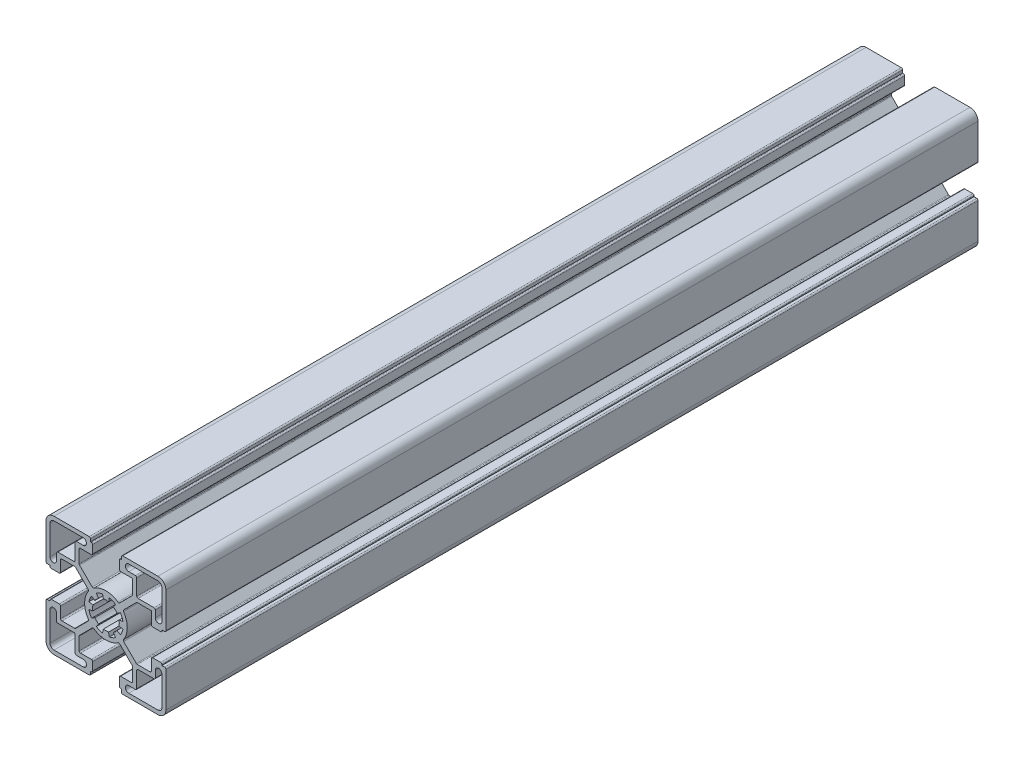
SolidWorks part; units mm, degrees
ref_plane "Front Plane" through (0, 0, 0) normal (0, 0, 1) x (1, 0, 0)
ref_plane "Top Plane" through (0, 0, 0) normal (0, 1, 0) x (1, 0, 0)
ref_plane "Right Plane" through (0, 0, 0) normal (1, 0, 0) x (0, 0, -1)
sketch "Sketch1" plane through (0, 0, 0) normal (0, 0, 1) x (1, 0, 0)
  line L0 (0, 22.5) -> (0, -22.5) construction
  line L1 (22.5, 0) -> (-22.5, 0) construction
  line L2 (-5.8, 22.5) -> (5.8, 22.5) construction
  line L3 (-5, 21) -> (5, 21) construction
  line L4 (-10.05, 10.05) -> (10.05, 10.05) construction
  line L5 (0, 0) -> (-10.05, 10.05) construction
  circle A0 centre (0, 0) radius 5 construction
  point P4 (0, 0)
  point P8 (0, 0)
  point P10 (0, 8)
  point P14 (0, 22.5)
  point P17 (0, 21)
  point P19 (0, 10.05)
sketch "Sketch2" plane through (0, 0, 0) normal (1, 0, 0) x (0, 0, -1)
  line L0 (152.4, 0) -> (-152.4, 0) construction
  point P4 (0, 0)
  dimension "D1" = 304.8
sketch "Sketch3" plane through (0, 0, 0) normal (0, 0, 1) x (1, 0, 0)
  line L5 (-21, 8.5375) -> (-21, 19.5)
  line L9 (0, 0) -> (-22.5, 22.5) construction
  line L10 (-11.55, -10.05) -> (-6.3569, -4.8569)
  line L11 (-19.5, 21) -> (-8.5375, 21)
  line L38 (-5.8, 22.5) -> (-5.8, 21)
  line L46 (-5.8, 21) -> (-5, 21)
  line L62 (-5, 21) -> (-5, 17.025)
  line L74 (-5, 17.025) -> (-10.05, 17.025)
  line L76 (-10.05, 17.025) -> (-10.05, 11.55)
  line L77 (-10.05, 11.55) -> (-4.8569, 6.3569)
  line L78 (-18.525, 8.5375) -> (-18.525, 11.55)
  line L79 (-10.05, 17.025) -> (-10.05, 22.5) construction
  line L80 (0, 22.5) -> (0, -22.5) construction
  line L81 (-5.8, 22.5) -> (5.8, 22.5) construction
  line L82 (10.05, 11.55) -> (4.8569, 6.3569)
  line L83 (10.05, 17.025) -> (10.05, 11.55)
  line L84 (5, 17.025) -> (10.05, 17.025)
  line L85 (5, 21) -> (5, 17.025)
  line L86 (5.8, 21) -> (5, 21)
  line L87 (5.8, 22.5) -> (5.8, 21)
  line L88 (-22.5, -5.8) -> (-21, -5.8)
  line L89 (-21, -5.8) -> (-21, -5)
  line L90 (-21, -5) -> (-17.025, -5)
  line L91 (-17.025, -5) -> (-17.025, -10.05)
  line L92 (-17.025, -10.05) -> (-11.55, -10.05)
  line L93 (-11.55, -10.05) -> (-6.3569, -4.8569)
  line L94 (-11.55, 10.05) -> (-6.3569, 4.8569)
  line L95 (-17.025, 10.05) -> (-11.55, 10.05)
  line L96 (-17.025, 5) -> (-17.025, 10.05)
  line L97 (-21, 5) -> (-17.025, 5)
  line L98 (-21, 5.8) -> (-21, 5)
  line L99 (-22.5, 5.8) -> (-21, 5.8)
  line L100 (-22.5, 5.8) -> (-22.5, 19.5)
  line L101 (-19.5, 22.5) -> (-5.8, 22.5)
  line L102 (-18.525, 11.55) -> (-11.55, 11.55)
  line L103 (-8.5375, 18.525) -> (-11.55, 18.525)
  line L104 (-11.55, 18.525) -> (-11.55, 11.55)
  line L108 (5.8, -22.5) -> (5.8, -21)
  line L113 (5.8, -21) -> (5, -21)
  line L117 (5.8, 22.5) -> (19.5, 22.5)
  line L118 (22.5, 19.5) -> (22.5, 5.8)
  line L119 (19.5, -22.5) -> (5.8, -22.5)
  line L120 (0, 0) -> (22.5, 0) construction
  line L121 (-22.5, -19.5) -> (-22.5, -5.8)
  line L136 (5, -21) -> (5, -17.025)
  line L137 (5, -17.025) -> (10.05, -17.025)
  line L138 (10.05, -17.025) -> (10.05, -11.55)
  line L139 (10.05, -11.55) -> (4.8569, -6.3569)
  line L140 (-10.05, -11.55) -> (-4.8569, -6.3569)
  line L141 (-10.05, -17.025) -> (-10.05, -11.55)
  line L142 (-5, -17.025) -> (-10.05, -17.025)
  line L143 (-5, -21) -> (-5, -17.025)
  line L144 (-5.8, -21) -> (-5, -21)
  line L145 (-5.8, -22.5) -> (-5.8, -21)
  line L146 (-5.8, -22.5) -> (-19.5, -22.5)
  line L147 (22.5, 5.8) -> (21, 5.8)
  line L148 (21, 5.8) -> (21, 5)
  line L149 (21, 5) -> (17.025, 5)
  line L150 (17.025, 5) -> (17.025, 10.05)
  line L151 (17.025, 10.05) -> (11.55, 10.05)
  line L152 (11.55, 10.05) -> (6.3569, 4.8569)
  line L153 (11.55, -10.05) -> (6.3569, -4.8569)
  line L154 (17.025, -10.05) -> (11.55, -10.05)
  line L155 (17.025, -5) -> (17.025, -10.05)
  line L156 (21, -5) -> (17.025, -5)
  line L157 (21, -5.8) -> (21, -5)
  line L158 (22.5, -5.8) -> (21, -5.8)
  line L159 (11.55, -10.05) -> (6.3569, -4.8569)
  line L160 (22.5, -5.8) -> (22.5, -19.5)
  line L161 (8.5375, 21) -> (19.5, 21)
  line L162 (21, 19.5) -> (21, 8.5375)
  line L163 (8.5375, 18.525) -> (11.55, 18.525)
  line L164 (11.55, 18.525) -> (11.55, 11.55)
  line L165 (18.525, 8.5375) -> (18.525, 11.55)
  line L166 (18.525, 11.55) -> (11.55, 11.55)
  line L167 (21, -8.5375) -> (21, -19.5)
  line L168 (19.5, -21) -> (8.5375, -21)
  line L169 (18.525, -8.5375) -> (18.525, -11.55)
  line L170 (18.525, -11.55) -> (11.55, -11.55)
  line L171 (8.5375, -18.525) -> (11.55, -18.525)
  line L172 (11.55, -18.525) -> (11.55, -11.55)
  line L173 (-8.5375, -21) -> (-19.5, -21)
  line L174 (-21, -19.5) -> (-21, -8.5375)
  line L175 (-8.5375, -18.525) -> (-11.55, -18.525)
  line L176 (-11.55, -18.525) -> (-11.55, -11.55)
  line L177 (-18.525, -8.5375) -> (-18.525, -11.55)
  line L178 (-18.525, -11.55) -> (-11.55, -11.55)
  line L179 (0, 0) -> (-11.55, 11.55) construction
  line L180 (0, 0) -> (11.55, 11.55) construction
  arc A2 (-21, 19.5) -> (-19.5, 21) centre (-19.5, 19.5) cw
  arc A73 (-4.8569, 6.3569) -> (4.8569, 6.3569) centre (0, 0) cw
  arc A74 (-6.3569, 4.8569) -> (-6.3569, -4.8569) centre (0, 0) ccw
  arc A75 (-19.5, 22.5) -> (-22.5, 19.5) centre (-19.5, 19.5) ccw
  arc A76 (-21, 8.5375) -> (-18.525, 8.5375) centre (-19.7625, 8.5375) ccw
  arc A77 (-8.5375, 21) -> (-8.5375, 18.525) centre (-8.5375, 19.7625) cw
  arc A80 (19.5, 22.5) -> (22.5, 19.5) centre (19.5, 19.5) cw
  arc A81 (22.5, -19.5) -> (19.5, -22.5) centre (19.5, -19.5) cw
  arc A82 (-19.5, -22.5) -> (-22.5, -19.5) centre (-19.5, -19.5) cw
  circle A88 centre (0, 0) radius 5 construction
  circle A89 centre (0, 0) radius 5
  arc A90 (-4.8569, -6.3569) -> (4.8569, -6.3569) centre (0, 0) ccw
  arc A91 (19.5, 21) -> (21, 19.5) centre (19.5, 19.5) cw
  arc A92 (6.3569, 4.8569) -> (6.3569, -4.8569) centre (0, 0) cw
  arc A93 (8.5375, 21) -> (8.5375, 18.525) centre (8.5375, 19.7625) ccw
  arc A94 (21, 8.5375) -> (18.525, 8.5375) centre (19.7625, 8.5375) cw
  arc A95 (21, -19.5) -> (19.5, -21) centre (19.5, -19.5) cw
  arc A96 (21, -8.5375) -> (18.525, -8.5375) centre (19.7625, -8.5375) ccw
  arc A97 (8.5375, -21) -> (8.5375, -18.525) centre (8.5375, -19.7625) cw
  arc A98 (-19.5, -21) -> (-21, -19.5) centre (-19.5, -19.5) cw
  arc A99 (-8.5375, -21) -> (-8.5375, -18.525) centre (-8.5375, -19.7625) ccw
  arc A100 (-21, -8.5375) -> (-18.525, -8.5375) centre (-19.7625, -8.5375) cw
  point P54 (-14.2875, 10.05)
  dimension "D2" = 3
  dimension "D3" = 1.5
  dimension "D4" = 1.5
  dimension "D5" = 1.5
  dimension "D6" = 90
  dimension "D1" = 4
extrude "Boss-Extrude1" add sketch "Sketch3" along normal up to vertex (152.4 mm away) and the other way up to vertex (152.4 mm away) contours A92 L152 L151 L150 L149 L148 L147 L118 A80 L117 L87 L86 L85 L84 L83 L82 A73 L77 L76 L74 L62 L46 L38 L101 A75 L100 L99 L98 L97 L96 L95 L94 A74 L10 L92 L91 L90 L89 L88 L121 A82 L146 L145 L144 L143 L142 L141 L140 A90 L139 L138 up to point (0, 0, 152.4) other way up to point (0, 0, -152.4)
fillet "Fillet1" radius 0.5 58 edges at (5, 21, 0) (5.8, 22.5, 0) (-5.8, 22.5, 0) (-5, 21, 0) (-10.05, 17.025, 0) (-5, 17.025, 0) (5, 17.025, 0) (-22.5, -5.8, 0) (-21, -5, 0) (-17.025, -5, 0) (-17.025, -10.05, 0) (-11.55, -10.05, 0) (-6.3569, -4.8569, 0) (-6.3569, 4.8569, 0) (-11.55, 10.05, 0) (-17.025, 10.05, 0) (-17.025, 5, 0) (-22.5, 5.8, 0) (-21, 5, 0) (-18.525, 11.55, 0) (-11.55, 11.55, 0) (-11.55, 18.525, 0) (4.8569, 6.3569, 0) (-4.8569, 6.3569, 0) (-10.05, 11.55, 0) (10.05, 17.025, 0) (10.05, 11.55, 0) (22.5, -5.8, 0) (21, -5, 0) (17.025, -5, 0) (17.025, -10.05, 0) (6.3569, 4.8569, 0) (11.55, 10.05, 0) (22.5, 5.8, 0) (21, 5, 0) (17.025, 5, 0) (4.8569, -6.3569, 0) (11.55, -11.55, 0) (-11.55, -11.55, 0) (18.525, -11.55, 0) (11.55, -18.525, 0) (10.05, -17.025, 0) (5, -17.025, 0) (5, -21, 0) (5.8, -22.5, 0) (-5.8, -22.5, 0) (-5, -21, 0) (-5, -17.025, 0) (-10.05, -17.025, 0) (-11.55, -18.525, 0) (11.55, 18.525, 0) (18.525, 11.55, 0) (11.55, 11.55, 0) (11.55, -10.05, 0) (6.3569, -4.8569, 0) (-4.8569, -6.3569, 0) (10.05, -11.55, 0) (-10.05, -11.55, 0)
sketch "Sketch4" plane through (0, 0, 152.4) normal (0, 0, 1) x (1, 0, 0)
  line L0 (-1.2681, 6.3751) -> (-0.9755, 4.9039)
  line L1 (0, 0) -> (0, 8) construction
  line L2 (-3.6112, 5.4046) -> (-2.7779, 4.1573)
  line L3 (1.2681, 6.3751) -> (0.9755, 4.9039)
  line L4 (3.6112, 5.4046) -> (2.7779, 4.1573)
  line L5 (5.4046, 3.6112) -> (4.1573, 2.7779)
  line L6 (6.3751, 1.2681) -> (4.9039, 0.9755)
  line L7 (6.3751, -1.2681) -> (4.9039, -0.9755)
  line L8 (5.4046, -3.6112) -> (4.1573, -2.7779)
  line L9 (3.6112, -5.4046) -> (2.7779, -4.1573)
  line L10 (1.2681, -6.3751) -> (0.9755, -4.9039)
  line L11 (-1.2681, -6.3751) -> (-0.9755, -4.9039)
  line L12 (-3.6112, -5.4046) -> (-2.7779, -4.1573)
  line L13 (-5.4046, -3.6112) -> (-4.1573, -2.7779)
  line L14 (-6.3751, -1.2681) -> (-4.9039, -0.9755)
  line L15 (-6.3751, 1.2681) -> (-4.9039, 0.9755)
  line L16 (-5.4046, 3.6112) -> (-4.1573, 2.7779)
  line L17 (0, 0) -> (-0.9755, 4.9039) construction
  line L18 (0, 0) -> (2.7779, 4.1573) construction
  arc A0 (-1.2681, 6.3751) -> (-3.6112, 5.4046) centre (0, 0) ccw
  circle A1 centre (0, 0) radius 5 construction
  arc A2 (-0.9755, 4.9039) -> (-2.7779, 4.1573) centre (0, 0) ccw
  arc A4 (2.7779, 4.1573) -> (0.9755, 4.9039) centre (0, 0) ccw
  arc A5 (3.6112, 5.4046) -> (1.2681, 6.3751) centre (0, 0) ccw
  arc A6 (4.9039, 0.9755) -> (4.1573, 2.7779) centre (0, 0) ccw
  arc A7 (6.3751, 1.2681) -> (5.4046, 3.6112) centre (0, 0) ccw
  arc A8 (4.1573, -2.7779) -> (4.9039, -0.9755) centre (0, 0) ccw
  arc A9 (5.4046, -3.6112) -> (6.3751, -1.2681) centre (0, 0) ccw
  arc A10 (0.9755, -4.9039) -> (2.7779, -4.1573) centre (0, 0) ccw
  arc A11 (1.2681, -6.3751) -> (3.6112, -5.4046) centre (0, 0) ccw
  arc A12 (-2.7779, -4.1573) -> (-0.9755, -4.9039) centre (0, 0) ccw
  arc A13 (-3.6112, -5.4046) -> (-1.2681, -6.3751) centre (0, 0) ccw
  arc A14 (-4.9039, -0.9755) -> (-4.1573, -2.7779) centre (0, 0) ccw
  arc A15 (-6.3751, -1.2681) -> (-5.4046, -3.6112) centre (0, 0) ccw
  arc A16 (-4.1573, 2.7779) -> (-4.9039, 0.9755) centre (0, 0) ccw
  arc A17 (-5.4046, 3.6112) -> (-6.3751, 1.2681) centre (0, 0) ccw
  dimension "D1" = 1.5
  dimension "D2" = 22.5
  dimension "D5" = 45
  dimension "D4" = 8
extrude "Cut-Extrude1" cut sketch "Sketch4" against normal through all
equation "\"D3@Sketch3\"=\"Wall@Sketch1\""
equation "\"D4@Sketch3\"=\"Wall@Sketch1\""
equation "\"D5@Sketch3\"=\"Wall@Sketch1\""
equation "\"D1@Sketch4\"=\"Wall@Sketch1\""
